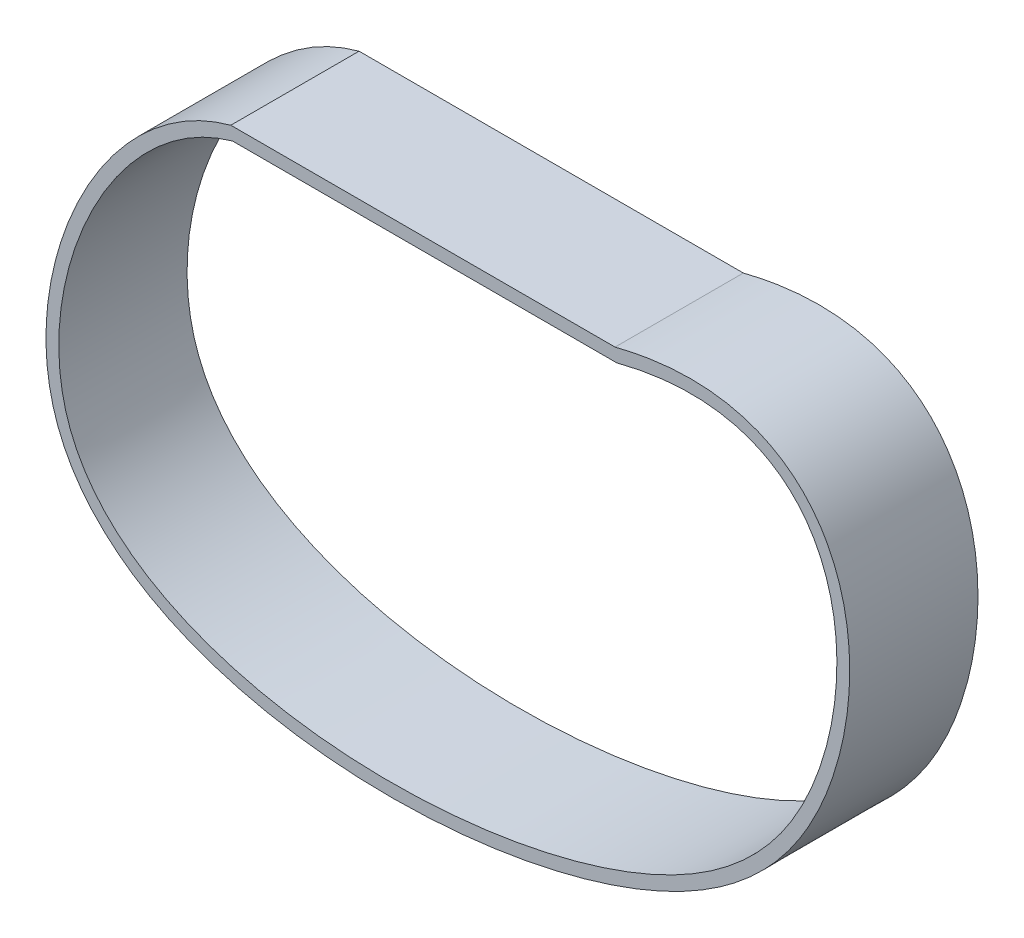
SolidWorks part; units mm, degrees
ref_plane "Front Plane" through (0, 0, 0) normal (0, 0, 1) x (1, 0, 0)
ref_plane "Top Plane" through (0, 0, 0) normal (0, 1, 0) x (1, 0, 0)
ref_plane "Right Plane" through (0, 0, 0) normal (1, 0, 0) x (0, 0, -1)
sketch "Sketch1" plane through (0, 0, 0) normal (0, 0, 1) x (1, 0, 0)
  line L0 (-28.836, 0) -> (31.059, 0)
  line L1 (-29.1095, 2) -> (30.806, 2)
  spline S0 degree 3 poles (31.059, 0) (68.4955, 9.7034) (72.2255, -44.302) (19.3538, -80.692) (-78.4239, -73.4294) (-47.7085, -5.2607) (-28.836, 0) knots 0 0 0 0 0.277881 0.417213 0.763853 1 1 1 1
  spline S1 degree 1 poles (30.806, 2) (-29.1095, 2) knots 0 0 1 1 construction
  spline S2 degree 3 poles (30.806, 2) (31.339, 2.1359) (32.4203, 2.3966) (34.502, 2.8387) (37.0194, 3.261) (39.8875, 3.5606) (43.5191, 3.6937) (47.7008, 3.3739) (52.1574, 2.2563) (56.044, 0.4553) (60.4443, -2.7639) (64.4423, -8.0867) (67.0128, -15.7897) (67.6683, -24.2382) (66.6524, -32.9503) (64.1625, -41.4489) (60.3601, -49.2465) (55.3956, -55.8641) (49.3729, -61.3851) (42.3973, -65.8979) (34.5692, -69.5137) (23.0723, -73.3205) (7.1408, -76.2381) (-12.5713, -76.5312) (-31.0172, -73.33) (-43.808, -67.432) (-51.4965, -60.469) (-55.6833, -54.0635) (-57.8849, -46.4554) (-58.101, -38.1472) (-56.6237, -29.5703) (-52.6174, -18.327) (-45.8905, -8.2134) (-38.0592, -1.9098) (-33.7086, 0.3804) (-31.4262, 1.2814) (-30.2695, 1.664) (-29.5884, 1.8674) (-29.2712, 1.9549) (-29.1095, 2) knots 0.000598 0.000598 0.000598 0.000598 0.004506 0.008414 0.016231 0.024047 0.031864 0.047496 0.063129 0.078762 0.094395 0.125661 0.156926 0.188192 0.219458 0.250723 0.281989 0.313255 0.34452 0.375786 0.407051 0.438317 0.500848 0.56338 0.625911 0.688442 0.719708 0.750974 0.782239 0.813505 0.844771 0.876036 0.938568 0.969833 0.985466 0.993283 0.997191 0.999145 1.001099 1.001099 1.001099 1.001099
  dimension "D1" = 2
extrude "Boss-Extrude1" add sketch "Sketch1" along normal mid plane 20
